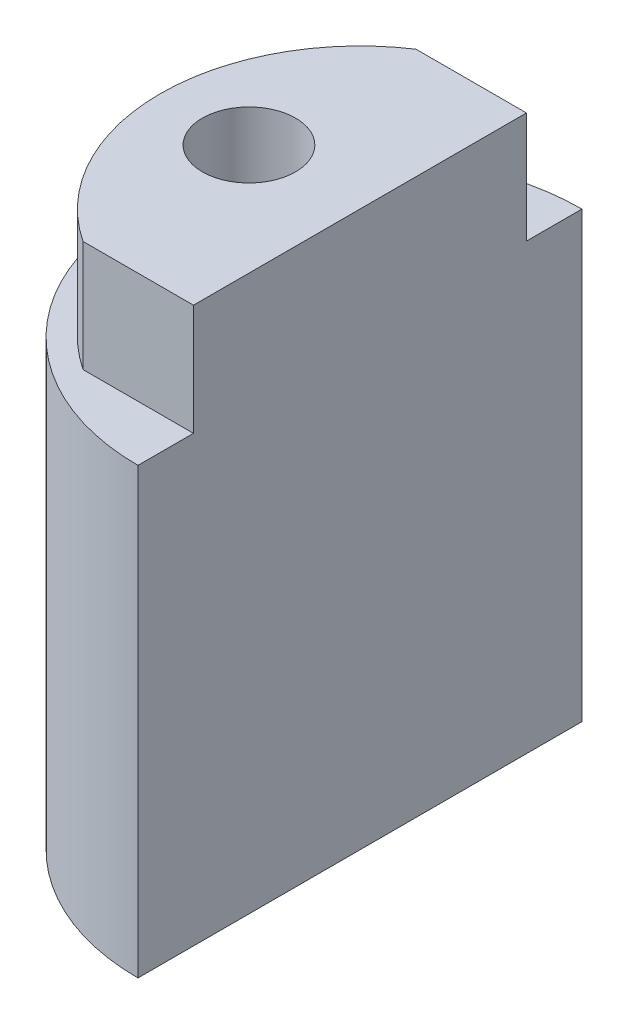
SolidWorks part; units mm, degrees
material "Brass"
ref_plane "Front Plane" through (0, 0, 0) normal (0, 0, 1) x (1, 0, 0)
ref_plane "Top Plane" through (0, 0, 0) normal (0, 1, 0) x (1, 0, 0)
ref_plane "Right Plane" through (0, 0, 0) normal (1, 0, 0) x (0, 0, -1)
sketch "Sketch1" plane through (0, 0, 0) normal (0, 1, 0) x (1, 0, 0)
  line L0 (0, 10) -> (0, -10)
  arc A4 (0, 10) -> (0, -10) centre (0, 0) ccw
  dimension "D1" = 20
extrude "Boss-Extrude1" add sketch "Sketch1" along normal blind 25
sketch "Sketch4" plane through (0, 25, 0) normal (0, 1, 0) x (1, 0, 0)
  circle A0 centre (0, 0) radius 3
  dimension "D1" = 6
sketch "Sketch18" plane through (0, 25, 0) normal (0, 1, 0) x (1, 0, 0)
  line L0 (0, 10) -> (0, -10)
  line L1 (0, 7.5) -> (-4.9749, 7.5)
  line L2 (0, -7.5) -> (-4.9749, -7.5)
  arc A1 (0, 10) -> (0, -10) centre (0, 0) ccw
  arc A2 (-4.9749, 7.5) -> (-4.9749, -7.5) centre (0, 0) ccw
  arc M6 (0, 10) -> (0, -10) centre (0, 0) ccw
  line M8 (0, -10) -> (0, 10)
  dimension "D1" = 7.5
  dimension "D2" = 20
  dimension "D4" = 9
  dimension "D3" = 7.5
extrude "Cut-Extrude1" cut sketch "Sketch18" against normal blind 5 contours L1 L0 M6 | L2 M8 M6
sketch "Sketch19" plane through (0, 25, 0) normal (0, 1, 0) x (1, 0, 0)
  line L0 (0, 0) -> (-10, 0) construction
  arc A0 (-6.6144, -7.5) -> (-6.6144, 7.5) centre (0, 0) ccw construction
hole_wizard "M5 Tapped Hole1" positions "Sketch20" profile "Sketch21" tap size "M5" standard "ISO"
sketch "Sketch20" plane through (0, 25, 0) normal (0, 1, 0) x (1, 0, 0)
  line L0 (0, 0) -> (-10, 0) construction
  point P0 (-5, 0)
sketch "Sketch21" plane through (-5, 25, 0) normal (1, 0, 0) x (0, 0, 1)
  line L0 (0, 0) -> (0, 12.4)
  line L1 (0, 12.4) -> (2.1, 11.1382)
  line L2 (2.1, 11.1382) -> (2.1, 0)
  line L5 (2.1, 0) -> (0, 0)
  line L10 (0, 12.4) -> (-2.1, 11.1382) construction
  line L11 (0, -6.35) -> (0, 107.95) construction
  dimension "Tap Drill Dia." = 4.2
  dimension "Tap Drill Depth" = 12.4
  dimension "Drill Angle" = 118
cosmetic thread "Hole Thread1" parameters "D1"=10, "D2"=5
